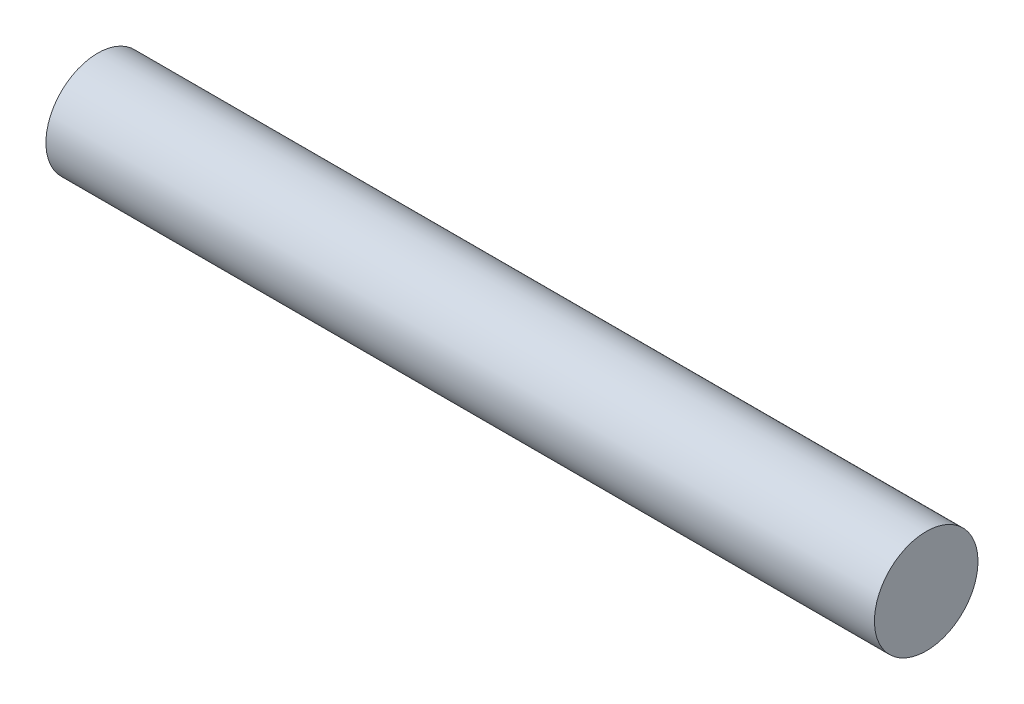
SolidWorks part; units mm, degrees
ref_plane "Front Plane" through (0, 0, 0) normal (0, 0, 1) x (1, 0, 0)
ref_plane "Top Plane" through (0, 0, 0) normal (0, 1, 0) x (1, 0, 0)
ref_plane "Right Plane" through (0, 0, 0) normal (1, 0, 0) x (0, 0, -1)
sketch "Sketch2" plane through (0, 0, 0) normal (1, 0, 0) x (0, 0, -1)
  circle A0 centre (0, 0) radius 1
  dimension "D1" = 2
extrude "Boss-Extrude1" add sketch "Sketch2" along normal blind 16
ref_plane "Plane1" through (8, 0, 0) normal (1, 0, 0) x (0, 0, -1)
